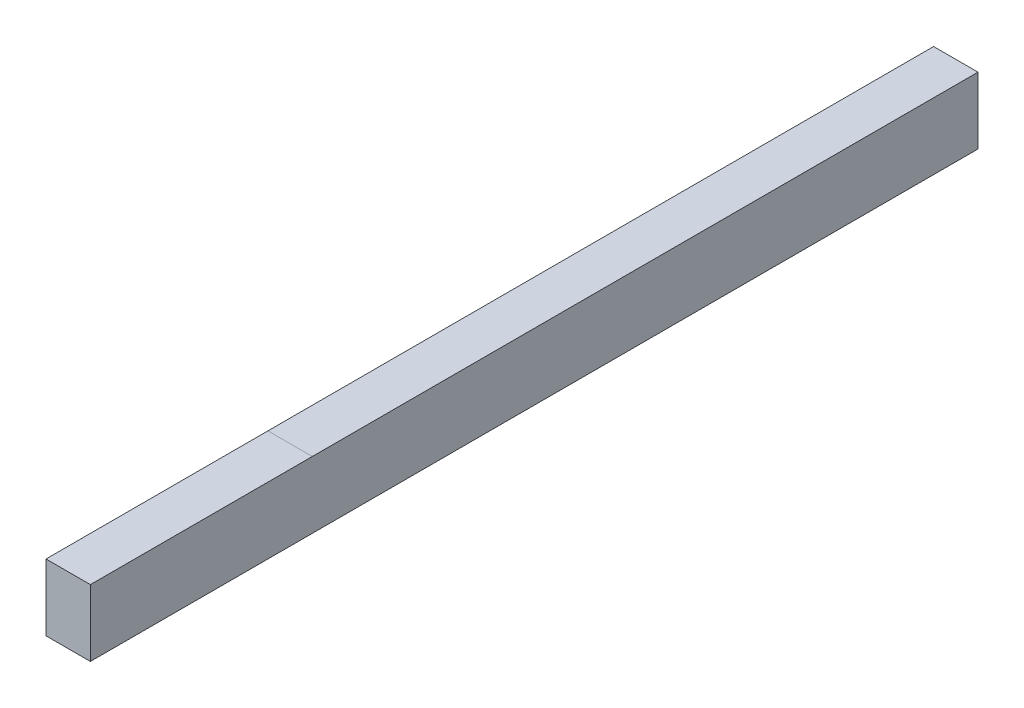
SolidWorks part; units mm, degrees
ref_plane "Płaszczyzna przednia" through (0, 0, 0) normal (0, 0, 1) x (1, 0, 0)
ref_plane "Płaszczyzna górna" through (0, 0, 0) normal (0, 1, 0) x (1, 0, 0)
ref_plane "Płaszczyzna prawa" through (0, 0, 0) normal (1, 0, 0) x (0, 0, -1)
sketch "Szkic1" plane through (0, 0, 0) normal (0, 0, 1) x (1, 0, 0)
  line L1 (0, 0) -> (10, 0)
  line L2 (0, 0) -> (0, 15)
  line L3 (0, 15) -> (10, 15)
  line L4 (10, 0) -> (10, 15)
  dimension "D1" = 15
  dimension "D2" = 10
extrude "Dodanie-wyciągnięcie1" add sketch "Szkic1" along normal blind 200
sketch "Szkic2" plane through (0, 15, 0) normal (0, 1, 0) x (1, 0, 0)
  line L0 (0, -150) -> (10, -150)
  line L1 (0, -200) -> (0, 0) construction
  line L2 (10, -200) -> (10, 0) construction
  line L3 (10, -200) -> (0, -200) construction
  dimension "D1" = 50
split line "Linia podziałowa1"
